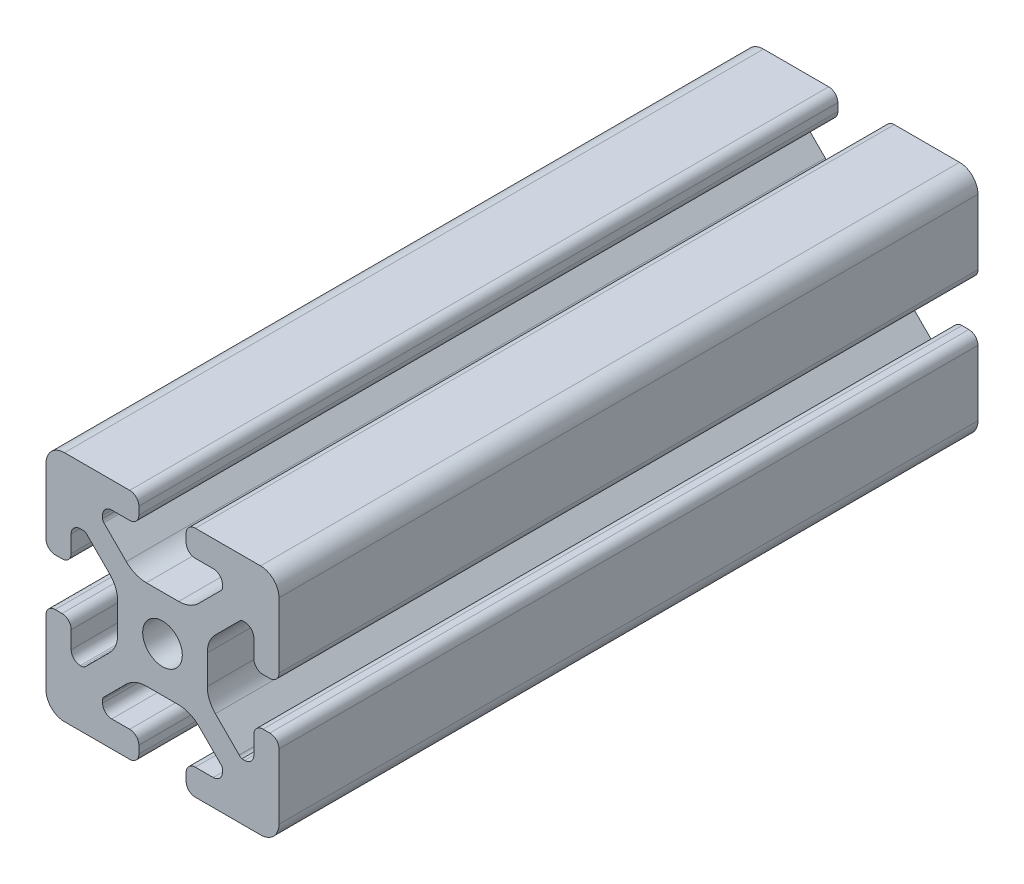
SolidWorks part; units mm, degrees
material "6105-T5 Aluminum"
ref_plane "Front Plane" through (0, 0, 0) normal (0, 0, 1) x (1, 0, 0)
ref_plane "Top Plane" through (0, 0, 0) normal (0, 1, 0) x (1, 0, 0)
ref_plane "Right Plane" through (0, 0, 0) normal (1, 0, 0) x (0, 0, -1)
sketch "Sketch1" plane through (0, 0, 0) normal (0, 0, 1) x (1, 0, 0)
  line L0 (0, 19.7407) -> (0, -19.7407) construction
  line L1 (19.0335, 0) -> (-20.7246, 0) construction
  line L2 (-8.715, -15.5246) -> (-5.63, -15.5246)
  line L3 (-10.285, -13.9546) -> (-10.285, -13.4925)
  line L4 (-6.2171, -9.1098) -> (-10.0624, -12.9551)
  line L5 (2.7773, -7.685) -> (-2.7773, -7.685)
  line L6 (10.0624, -12.9551) -> (6.2171, -9.1098)
  line L7 (10.285, -13.9546) -> (10.285, -13.4925)
  line L8 (5.63, -15.5246) -> (8.715, -15.5246)
  line L9 (4.06, -18.43) -> (4.06, -17.0946)
  line L10 (-4.06, -18.43) -> (-4.06, -17.0946)
  line L11 (15.68, -8.7154) -> (15.68, -5.63)
  line L12 (-14.11, -10.2854) -> (-13.8169, -10.2854)
  line L13 (20, -16.83) -> (20, -5.63)
  line L14 (20, 5.63) -> (20, 13.0011)
  line L15 (-16.83, 20) -> (-5.63, 20)
  line L16 (5.63, 20) -> (12.9796, 20)
  line L18 (-8.715, 15.5246) -> (-5.63, 15.5246)
  line L19 (-20, -17.0184) -> (-20, -5.7579)
  line L20 (-20, 5.573) -> (-20, 13.0045)
  line L21 (-15.68, -8.7154) -> (-15.68, -5.7579)
  line L23 (-16.6746, -20) -> (-5.63, -20)
  line L24 (5.63, -20) -> (13, -20)
  line L53 (14.11, -10.2854) -> (13.6201, -10.2854)
  line L54 (13.1637, -9.947) -> (9.0762, -5.8595)
  line L55 (7.685, -2.5008) -> (7.685, 2.5008)
  line L56 (9.0762, 5.8595) -> (13.2795, 10.0628)
  line L57 (13.8169, 10.2854) -> (14.11, 10.2854)
  line L58 (15.68, 8.7154) -> (15.68, 5.63)
  line L59 (17.25, 4.06) -> (18.43, 4.06)
  line L61 (20, 13.0011) -> (20, 16.83)
  line L62 (16.83, 20) -> (12.9796, 20)
  line L64 (4.06, 18.43) -> (4.06, 17.0946)
  line L65 (5.63, 15.5246) -> (8.715, 15.5246)
  line L66 (10.285, 13.9546) -> (10.285, 13.4925)
  line L67 (10.0624, 12.9551) -> (6.2171, 9.1098)
  line L68 (2.7773, 7.685) -> (-2.7773, 7.685)
  line L69 (-6.2171, 9.1098) -> (-10.0624, 12.9551)
  line L70 (-10.285, 13.4925) -> (-10.285, 13.9546)
  line L72 (-4.06, 17.0946) -> (-4.06, 18.43)
  line L75 (-20, 16.83) -> (-20, 13.0045)
  line L77 (-18.43, 4.003) -> (-17.25, 4.003)
  line L78 (-15.68, 5.573) -> (-15.68, 8.4757)
  line L79 (-14.0552, 10.0447) -> (-13.7199, 10.033)
  line L80 (-13.0405, 9.8238) -> (-9.0762, 5.8595)
  line L81 (-7.685, 2.5008) -> (-7.685, -2.5008)
  line L82 (-9.0762, -5.8595) -> (-13.2795, -10.0628)
  line L85 (-17.25, -4.1204) -> (-18.43, -4.1204)
  line L100 (13, -20) -> (16.83, -20)
  line L103 (18.43, -4.06) -> (17.25, -4.06)
  arc A0 (-5.63, -15.5246) -> (-4.06, -17.0946) centre (-5.63, -17.0946) cw
  arc A1 (-8.715, -15.5246) -> (-10.285, -13.9546) centre (-8.715, -13.9546) cw
  arc A2 (-10.285, -13.4925) -> (-10.0624, -12.9551) centre (-9.525, -13.4925) cw
  arc A3 (-6.2171, -9.1098) -> (-2.7773, -7.685) centre (-2.7773, -12.5496) cw
  arc A4 (2.7773, -7.685) -> (6.2171, -9.1098) centre (2.7773, -12.5496) cw
  arc A5 (10.0624, -12.9551) -> (10.285, -13.4925) centre (9.525, -13.4925) cw
  arc A6 (10.285, -13.9546) -> (8.715, -15.5246) centre (8.715, -13.9546) cw
  arc A7 (4.06, -17.0946) -> (5.63, -15.5246) centre (5.63, -17.0946) cw
  arc A8 (5.63, -20) -> (4.06, -18.43) centre (5.63, -18.43) cw
  arc A9 (-4.06, -18.43) -> (-5.63, -20) centre (-5.63, -18.43) cw
  circle A45 centre (0, 0) radius 3.4
  arc A46 (17.25, -4.06) -> (15.68, -5.63) centre (17.25, -5.63) ccw
  arc A47 (14.11, -10.2854) -> (15.68, -8.7154) centre (14.11, -8.7154) ccw
  arc A48 (13.1637, -9.947) -> (13.6201, -10.2854) centre (13.8117, -9.55) ccw
  arc A49 (7.685, -2.5008) -> (9.0762, -5.8595) centre (12.435, -2.5008) ccw
  arc A50 (9.0762, 5.8595) -> (7.685, 2.5008) centre (12.435, 2.5008) ccw
  arc A51 (13.8169, 10.2854) -> (13.2795, 10.0628) centre (13.8169, 9.5254) ccw
  arc A52 (15.68, 8.7154) -> (14.11, 10.2854) centre (14.11, 8.7154) ccw
  arc A53 (15.68, 5.63) -> (17.25, 4.06) centre (17.25, 5.63) ccw
  arc A54 (18.43, 4.06) -> (20, 5.63) centre (18.43, 5.63) ccw
  arc A55 (20, 16.83) -> (16.83, 20) centre (16.83, 16.83) ccw
  arc A56 (5.63, 20) -> (4.06, 18.43) centre (5.63, 18.43) ccw
  arc A57 (4.06, 17.0946) -> (5.63, 15.5246) centre (5.63, 17.0946) ccw
  arc A58 (10.285, 13.9546) -> (8.715, 15.5246) centre (8.715, 13.9546) ccw
  arc A59 (10.0624, 12.9551) -> (10.285, 13.4925) centre (9.525, 13.4925) ccw
  arc A60 (2.7773, 7.685) -> (6.2171, 9.1098) centre (2.7773, 12.5496) ccw
  arc A61 (-6.2171, 9.1098) -> (-2.7773, 7.685) centre (-2.7773, 12.5496) ccw
  arc A62 (-10.285, 13.4925) -> (-10.0624, 12.9551) centre (-9.525, 13.4925) ccw
  arc A63 (-8.715, 15.5246) -> (-10.285, 13.9546) centre (-8.715, 13.9546) ccw
  arc A64 (-5.63, 15.5246) -> (-4.06, 17.0946) centre (-5.63, 17.0946) ccw
  arc A65 (-4.06, 18.43) -> (-5.63, 20) centre (-5.63, 18.43) ccw
  arc A66 (-16.83, 20) -> (-20, 16.83) centre (-16.83, 16.83) ccw
  arc A67 (-20, 5.573) -> (-18.43, 4.003) centre (-18.43, 5.573) ccw
  arc A68 (-17.25, 4.003) -> (-15.68, 5.573) centre (-17.25, 5.573) ccw
  arc A69 (-14.0552, 10.0447) -> (-15.68, 8.4757) centre (-14.11, 8.4757) ccw
  arc A70 (-13.0405, 9.8238) -> (-13.7199, 10.033) centre (-13.5779, 9.2864) ccw
  arc A71 (-7.685, 2.5008) -> (-9.0762, 5.8595) centre (-12.435, 2.5008) ccw
  arc A72 (-9.0762, -5.8595) -> (-7.685, -2.5008) centre (-12.435, -2.5008) ccw
  arc A73 (-13.8169, -10.2854) -> (-13.2795, -10.0628) centre (-13.8169, -9.5254) ccw
  arc A74 (-15.68, -8.7154) -> (-14.11, -10.2854) centre (-14.11, -8.7154) ccw
  arc A75 (-15.68, -5.7579) -> (-17.25, -4.1204) centre (-17.2485, -5.6904) ccw
  arc A76 (-18.43, -4.1204) -> (-20, -5.7579) centre (-18.4315, -5.6904) ccw
  arc A77 (-20, -17.0184) -> (-16.6746, -20) centre (-16.8354, -16.8341) ccw
  arc A88 (16.83, -20) -> (20, -16.83) centre (16.83, -16.83) ccw
  arc A89 (20, -5.63) -> (18.43, -4.06) centre (18.43, -5.63) ccw
  dimension "D2" = 6.8
  dimension "D7" = 20.57
  dimension "D1" = 40
  dimension "D3" = 4.32
  dimension "D4" = 15.37
  dimension "D5" = 20
  dimension "D6" = 4.32
  dimension "D9" = 15.37
extrude "Extrude1" add sketch "Sketch1" against normal blind 120
